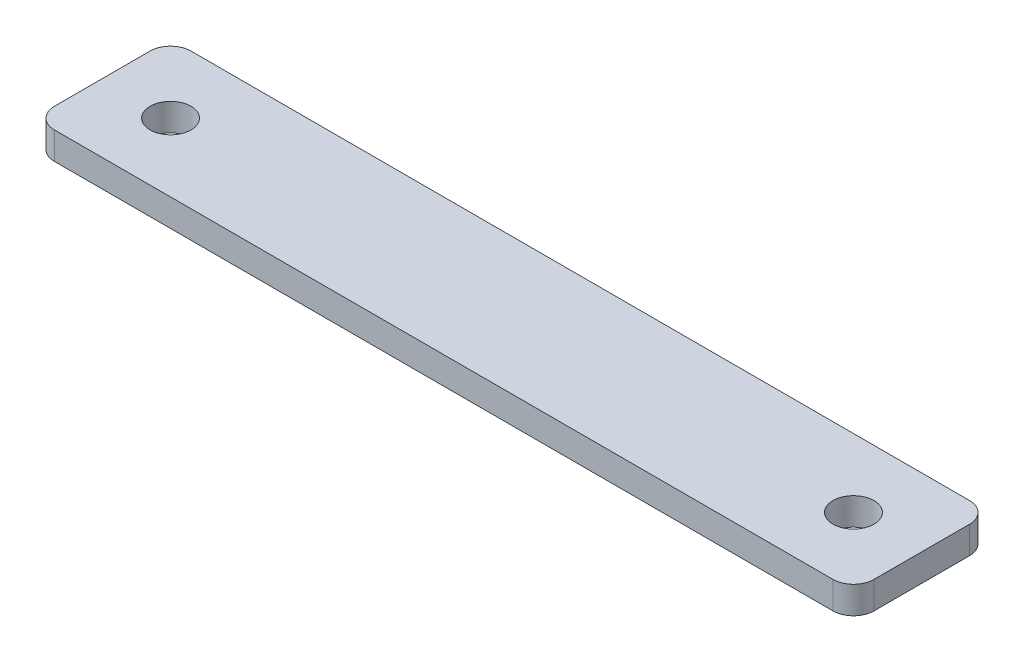
SolidWorks part; units mm, degrees
ref_plane "Front Plane" through (0, 0, 0) normal (0, 0, 1) x (1, 0, 0)
ref_plane "Top Plane" through (0, 0, 0) normal (0, 1, 0) x (1, 0, 0)
ref_plane "Right Plane" through (0, 0, 0) normal (1, 0, 0) x (0, 0, -1)
sketch "Sketch1" plane through (0, 0, 0) normal (0, 1, 0) x (1, 0, 0)
  line L1 (-60, -10) -> (60, -10)
  line L2 (-60, -10) -> (-60, 10)
  line L3 (-60, 10) -> (60, 10)
  line L4 (60, -10) -> (60, 10)
  line L5 (-60, -10) -> (60, 10) construction
  line L6 (-60, 10) -> (60, -10) construction
  point P0 (0, 0)
  dimension "D1" = 120
  dimension "D2" = 20
extrude "Boss-Extrude1" add sketch "Sketch1" along normal blind 4
sketch "Sketch2" plane through (0, 4, 0) normal (0, 1, 0) x (1, 0, 0)
  line L0 (60, 10) -> (-60, 10) construction
  line L1 (-60, 10) -> (-60, -10) construction
  circle A0 centre (-50, 0) radius 3
  circle A1 centre (50, 0) radius 3
  dimension "D1" = 10
  dimension "D2" = 10
extrude "Cut-Extrude1" cut sketch "Sketch2" against normal blind 4
fillet "Fillet1" radius 3 4 edges at (-60, 2, 10) (-60, 2, -10) (60, 2, 10) (60, 2, -10)
